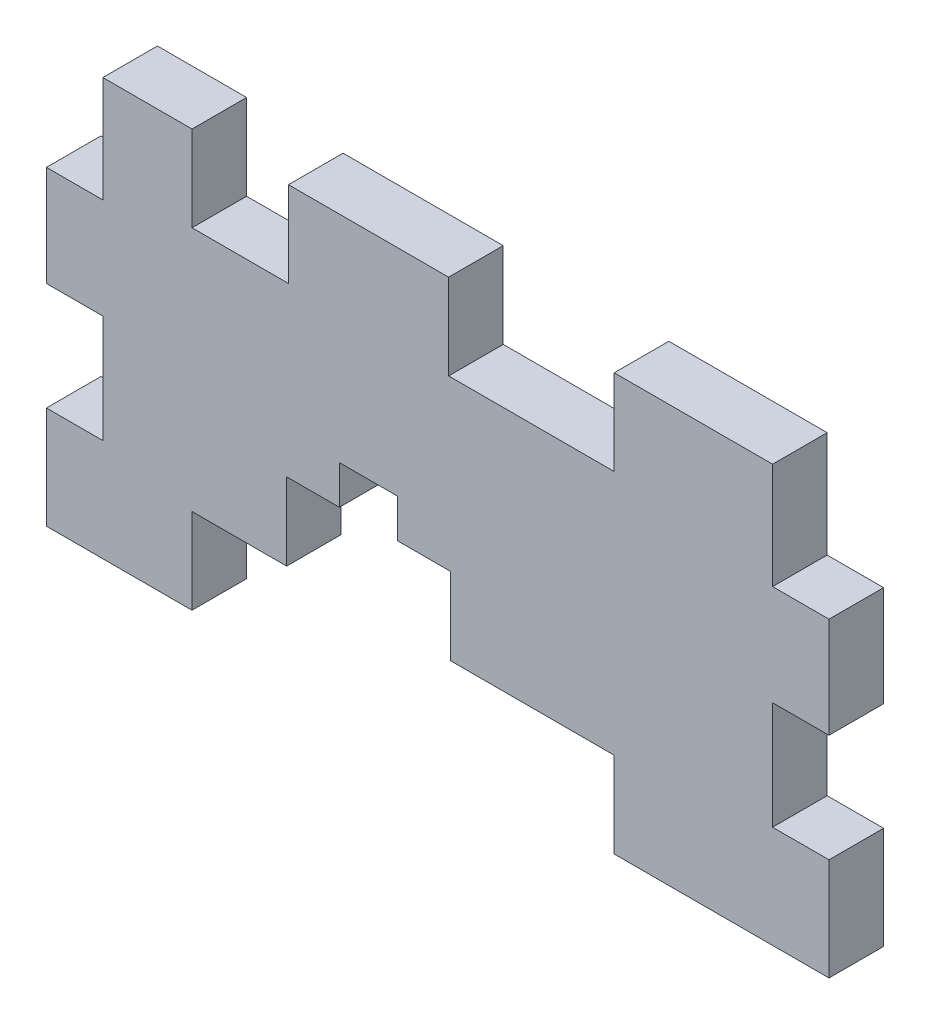
SolidWorks part; units mm, degrees
ref_plane "Front Plane" through (0, 0, 0) normal (0, 0, 1) x (1, 0, 0)
ref_plane "Top Plane" through (0, 0, 0) normal (0, 1, 0) x (1, 0, 0)
ref_plane "Right Plane" through (0, 0, 0) normal (1, 0, 0) x (0, 0, -1)
sketch "Sketch1" plane through (0, 0, 0) normal (0, 0, 1) x (1, 0, 0)
  line L0 (21.5, 33.35) -> (21.5, 15.05) construction
  line L1 (21.5, 37.95) -> (-21.5, 37.95)
  line L2 (21.5, 37.95) -> (21.5, 15.05)
  line L3 (21.5, 15.05) -> (0.7, 15.05)
  line L4 (-21.5, 37.95) -> (-21.5, 15.05)
  line L5 (-21.5, 33.35) -> (-21.5, 15.05) construction
  line L6 (32.157, 37.95) -> (-32.157, 37.95) construction
  line L7 (28.5, 15.05) -> (-28.5, 15.05) construction
  line L8 (0.7, 15.05) -> (0.7, 24) construction
  line L9 (0.7, 24) -> (-8.3, 24) construction
  line L10 (-8.3, 24) -> (-8.3, 15.05) construction
  line L11 (0.7, 15.05) -> (0.7, 24)
  line L12 (0.7, 24) -> (-8.3, 24)
  line L13 (-8.3, 24) -> (-8.3, 15.05)
  line L14 (-8.3, 15.05) -> (-21.5, 15.05)
sketch "Sketch2" plane through (0, 0, 0) normal (1, 0, 0) x (0, 0, -1)
  line L0 (0, 19.65) -> (0, 37.95) construction
  line L1 (0, 37.95) -> (-3, 37.95)
  line L2 (0, 37.95) -> (0, 15.05)
  line L3 (0, 15.05) -> (-3, 15.05)
  line L4 (-3, 37.95) -> (-3, 15.05)
  line L5 (-3, 19.65) -> (-3, 34.95) construction
  line L6 (-53.657, 15.05) -> (10.657, 15.05) construction
  line L7 (-50, 37.95) -> (7, 37.95) construction
extrude "Boss-Extrude1" add sketch "Sketch1" along normal up to vertex (3 mm away) up to point (0, 37.95, 3)
sketch "Sketch3" plane through (0, 0, 0) normal (0, 0, 1) x (1, 0, 0)
  line L0 (32.157, 37.95) -> (-32.157, 37.95) construction
  line L1 (21.5, 37.95) -> (-21.5, 37.95) construction
  line L2 (21.5, 37.95) -> (21.5, 15.05) construction
  line L3 (21.5, 15.05) -> (0.7, 15.05) construction
  line L4 (-21.5, 37.95) -> (-21.5, 15.05) construction
  line L5 (0.7, 15.05) -> (0.7, 24) construction
  line L6 (0.7, 24) -> (-8.3, 24) construction
  line L7 (-8.3, 24) -> (-8.3, 15.05) construction
  line L8 (0.7, 24) -> (-8.3, 24) construction
  line L9 (-8.3, 24) -> (-8.3, 15.05) construction
  line L10 (-13.4, 15.05) -> (-13.4, 37.95) construction
  line L11 (0.7, 15.05) -> (0.7, 24) construction
  line L12 (-8.3, 15.05) -> (-21.5, 15.05) construction
  line L13 (32.157, 26.5) -> (-32.157, 26.5) construction
  line L14 (32.157, 26.5) -> (-32.157, 26.5) construction
  line L15 (0, 15.05) -> (0, 37.95) construction
  line L16 (0, 15.05) -> (0, 37.95) construction
  line L17 (32.157, 33.35) -> (-32.157, 33.35) construction
  line L18 (32.157, 34.15) -> (-32.157, 34.15) construction
  line L19 (32.157, 37.15) -> (-32.157, 37.15) construction
  line L20 (21.5, 33.35) -> (-21.5, 33.35) construction
  line L21 (21.5, 34.15) -> (-21.5, 34.15) construction
  line L22 (21.5, 37.15) -> (-21.5, 37.15) construction
  line L23 (28.5, 19.65) -> (-28.5, 19.65) construction
  line L24 (28.5, 18.85) -> (0.7, 18.85) construction
  line L25 (-8.3, 18.85) -> (-28.5, 18.85) construction
  line L26 (-8.3, 15.85) -> (-28.5, 15.85) construction
  line L27 (28.5, 15.85) -> (0.7, 15.85) construction
  line L28 (21.5, 19.65) -> (0.7, 19.65) construction
  line L29 (21.5, 18.85) -> (0.7, 18.85) construction
  line L30 (-8.3, 18.85) -> (-21.5, 18.85) construction
  line L31 (-8.3, 15.85) -> (-21.5, 15.85) construction
  line L32 (21.5, 15.85) -> (0.7, 15.85) construction
  line L33 (-8.3, 19.65) -> (-21.5, 19.65) construction
  line L34 (-18.5, 15.05) -> (-18.5, 37.95) construction
  line L35 (21.5, 37.95) -> (18.5, 37.95)
  line L36 (21.5, 37.95) -> (21.5, 32.225)
  line L37 (21.5, 32.225) -> (18.5, 32.225)
  line L38 (18.5, 37.95) -> (18.5, 32.225)
  line L39 (21.5, 26.5) -> (18.5, 26.5)
  line L40 (21.5, 26.5) -> (21.5, 20.775)
  line L41 (21.5, 20.775) -> (18.5, 20.775)
  line L42 (18.5, 26.5) -> (18.5, 20.775)
  line L43 (18.5, 15.05) -> (18.5, 37.95) construction
  line L44 (18.5, 18.05) -> (18.5, 33.35) construction
  line L45 (-18.5, 33.35) -> (-18.5, 18.05) construction
  line L46 (20, 26.5) -> (20, 32.225) construction
  line L47 (-18.5, 20.775) -> (-13.4, 20.775) construction
  line L48 (-13.4, 20.775) -> (-8.3, 20.775) construction
  line L49 (9.6, 15.05) -> (9.6, 37.95) construction
  line L50 (0.7, 24) -> (0.7, 15.05) construction
  line L51 (-8.3, 37.95) -> (-13.4, 37.95)
  line L52 (18.5, 20.775) -> (9.6, 20.775) construction
  line L53 (9.6, 20.775) -> (0.7, 20.775) construction
  line L54 (9.6, 37.95) -> (0.7, 37.95)
  line L55 (9.6, 37.95) -> (9.6, 33.35)
  line L56 (-3.8, 28.05) -> (-3.8, 26.025) construction
  line L57 (-3.8, 26.025) -> (-3.8, 24) construction
  line L58 (-2.3, 26.025) -> (-5.3, 26.025)
  line L59 (-5.3, 26.025) -> (-5.3, 24)
  line L60 (-2.3, 26.025) -> (-2.3, 24)
  line L61 (9.6, 33.35) -> (0.7, 33.35)
  line L62 (-13.4, 37.95) -> (-13.4, 33.35)
  line L63 (9.6, 15.05) -> (-13.4, 15.05)
  line L64 (9.6, 15.05) -> (9.6, 19.65)
  line L65 (9.6, 19.65) -> (-13.4, 19.65)
  line L66 (-13.4, 15.05) -> (-13.4, 19.65)
  line L67 (-8.3, 33.35) -> (-13.4, 33.35)
  line L68 (-21.5, 15.05) -> (-21.5, 24.95) construction
  line L69 (-2.3, 37.95) -> (-2.3, 15.05) construction
  line L70 (0.7, 37.95) -> (0.7, 33.35)
  line L71 (-8.3, 37.95) -> (-8.3, 33.35)
  line L72 (28.5, 15.05) -> (-28.5, 15.05) construction
  line L75 (-21.5, 37.95) -> (-18.5, 37.95)
  line L76 (-21.5, 37.95) -> (-21.5, 32.225)
  line L77 (-21.5, 32.225) -> (-18.5, 32.225)
  line L78 (-18.5, 37.95) -> (-18.5, 32.225)
  line L79 (-21.5, 26.5) -> (-18.5, 26.5)
  line L80 (-21.5, 26.5) -> (-21.5, 20.775)
  line L81 (-21.5, 20.775) -> (-18.5, 20.775)
  line L82 (-18.5, 26.5) -> (-18.5, 20.775)
  line L84 (-5.3, 37.95) -> (-5.3, 15.05) construction
  line L85 (-2.3, 15.05) -> (-2.3, 21) construction
  line L86 (-5.3, 21) -> (-5.3, 15.05) construction
  line L87 (-2.3, 28.05) -> (-5.3, 28.05) construction
  line L89 (-2.3, 24) -> (-5.3, 24)
sketch "Sketch4" plane through (0, 0, 0) normal (0, 0, 1) x (1, 0, 0)
  line L0 (21.6, 26.6) -> (18.4, 26.6)
  line L1 (18.4, 26.6) -> (18.4, 20.675)
  line L2 (18.4, 20.675) -> (21.6, 20.675)
  line L3 (21.6, 20.675) -> (21.6, 26.6)
  line L4 (21.5, 26.5) -> (18.5, 26.5)
  line L5 (18.5, 26.5) -> (18.5, 20.775)
  line L6 (18.5, 20.775) -> (21.5, 20.775)
  line L7 (21.5, 20.775) -> (21.5, 26.5)
  line L8 (21.5, 26.5) -> (18.5, 26.5) construction
  line L9 (18.5, 26.5) -> (18.5, 20.775) construction
  line L10 (18.5, 20.775) -> (21.5, 20.775) construction
  line L11 (21.5, 20.775) -> (21.5, 26.5) construction
  line L12 (21.5, 37.95) -> (18.5, 37.95)
  line L13 (21.5, 32.225) -> (21.5, 37.95)
  line L14 (18.5, 32.225) -> (21.5, 32.225)
  line L15 (18.5, 37.95) -> (18.5, 32.225)
  line L16 (21.5, 37.95) -> (18.5, 37.95) construction
  line L17 (21.5, 32.225) -> (21.5, 37.95) construction
  line L18 (18.5, 32.225) -> (21.5, 32.225) construction
  line L19 (18.5, 37.95) -> (18.5, 32.225) construction
  line L20 (9.6, 19.65) -> (-13.4, 19.65)
  line L21 (-13.4, 19.65) -> (-13.4, 15.05)
  line L22 (-13.4, 15.05) -> (9.6, 15.05)
  line L23 (9.6, 15.05) -> (9.6, 19.65)
  line L24 (9.6, 19.65) -> (-13.4, 19.65) construction
  line L25 (-13.4, 19.65) -> (-13.4, 15.05) construction
  line L26 (-13.4, 15.05) -> (9.6, 15.05) construction
  line L27 (9.6, 15.05) -> (9.6, 19.65) construction
  line L28 (9.6, 37.95) -> (0.7, 37.95)
  line L29 (9.6, 33.35) -> (9.6, 37.95)
  line L30 (0.7, 33.35) -> (9.6, 33.35)
  line L31 (0.7, 37.95) -> (0.7, 33.35)
  line L32 (9.6, 37.95) -> (0.7, 37.95) construction
  line L33 (9.6, 33.35) -> (9.6, 37.95) construction
  line L34 (0.7, 33.35) -> (9.6, 33.35) construction
  line L35 (0.7, 37.95) -> (0.7, 33.35) construction
  line L36 (-18.5, 26.5) -> (-21.5, 26.5)
  line L37 (-18.5, 20.775) -> (-18.5, 26.5)
  line L38 (-21.5, 20.775) -> (-18.5, 20.775)
  line L39 (-21.5, 26.5) -> (-21.5, 20.775)
  line L40 (-18.5, 26.5) -> (-21.5, 26.5) construction
  line L41 (-18.5, 20.775) -> (-18.5, 26.5) construction
  line L42 (-21.5, 20.775) -> (-18.5, 20.775) construction
  line L43 (-21.5, 26.5) -> (-21.5, 20.775) construction
  line L44 (-21.5, 32.225) -> (-18.5, 32.225)
  line L45 (-18.5, 32.225) -> (-18.5, 37.95)
  line L46 (-18.5, 37.95) -> (-21.5, 37.95)
  line L47 (-21.5, 37.95) -> (-21.5, 32.225)
  line L48 (-21.5, 32.225) -> (-18.5, 32.225) construction
  line L49 (-18.5, 32.225) -> (-18.5, 37.95) construction
  line L50 (-18.5, 37.95) -> (-21.5, 37.95) construction
  line L51 (-21.5, 37.95) -> (-21.5, 32.225) construction
  line L52 (-13.4, 33.35) -> (-8.3, 33.35)
  line L53 (-13.4, 37.95) -> (-13.4, 33.35)
  line L54 (-8.3, 37.95) -> (-13.4, 37.95)
  line L55 (-8.3, 33.35) -> (-8.3, 37.95)
  line L56 (-13.4, 33.35) -> (-8.3, 33.35) construction
  line L57 (-13.4, 37.95) -> (-13.4, 33.35) construction
  line L58 (-8.3, 37.95) -> (-13.4, 37.95) construction
  line L59 (-8.3, 33.35) -> (-8.3, 37.95) construction
  line L60 (-5.3, 26.025) -> (-5.3, 24)
  line L61 (-2.3, 26.025) -> (-5.3, 26.025)
  line L62 (-2.3, 24) -> (-2.3, 26.025)
  line L63 (-5.3, 24) -> (-2.3, 24)
  line L64 (-5.3, 26.025) -> (-5.3, 24) construction
  line L65 (-2.3, 26.025) -> (-5.3, 26.025) construction
  line L66 (-2.3, 24) -> (-2.3, 26.025) construction
  line L67 (-5.3, 24) -> (-2.3, 24) construction
  line L68 (21.6, 38.05) -> (18.4, 38.05)
  line L69 (18.4, 38.05) -> (18.4, 32.125)
  line L70 (18.4, 32.125) -> (21.6, 32.125)
  line L71 (21.6, 32.125) -> (21.6, 38.05)
  line L72 (9.7, 19.75) -> (-13.5, 19.75)
  line L73 (-13.5, 19.75) -> (-13.5, 14.95)
  line L74 (-13.5, 14.95) -> (9.7, 14.95)
  line L75 (9.7, 14.95) -> (9.7, 19.75)
  line L76 (9.7, 38.05) -> (0.6, 38.05)
  line L77 (0.6, 38.05) -> (0.6, 33.25)
  line L78 (0.6, 33.25) -> (9.7, 33.25)
  line L79 (9.7, 33.25) -> (9.7, 38.05)
  line L80 (-18.4, 26.6) -> (-21.6, 26.6)
  line L81 (-21.6, 26.6) -> (-21.6, 20.675)
  line L82 (-21.6, 20.675) -> (-18.4, 20.675)
  line L83 (-18.4, 20.675) -> (-18.4, 26.6)
  line L84 (-21.6, 32.125) -> (-18.4, 32.125)
  line L85 (-18.4, 32.125) -> (-18.4, 38.05)
  line L86 (-18.4, 38.05) -> (-21.6, 38.05)
  line L87 (-21.6, 38.05) -> (-21.6, 32.125)
  line L88 (-13.5, 33.25) -> (-8.2, 33.25)
  line L89 (-8.2, 33.25) -> (-8.2, 38.05)
  line L90 (-8.2, 38.05) -> (-13.5, 38.05)
  line L91 (-13.5, 38.05) -> (-13.5, 33.25)
  line L92 (-5.4, 26.125) -> (-5.4, 23.9)
  line L93 (-5.4, 23.9) -> (-2.2, 23.9)
  line L94 (-2.2, 23.9) -> (-2.2, 26.125)
  line L95 (-2.2, 26.125) -> (-5.4, 26.125)
  dimension "D1" = 0
  dimension "D2" = 0
  dimension "D3" = 0
  dimension "D4" = 0
  dimension "D5" = 0
  dimension "D6" = 0
  dimension "D7" = 0
  dimension "D8" = 0
  dimension "D9" = 0.1
extrude "Cut-Extrude2" cut sketch "Sketch4" along normal through all
